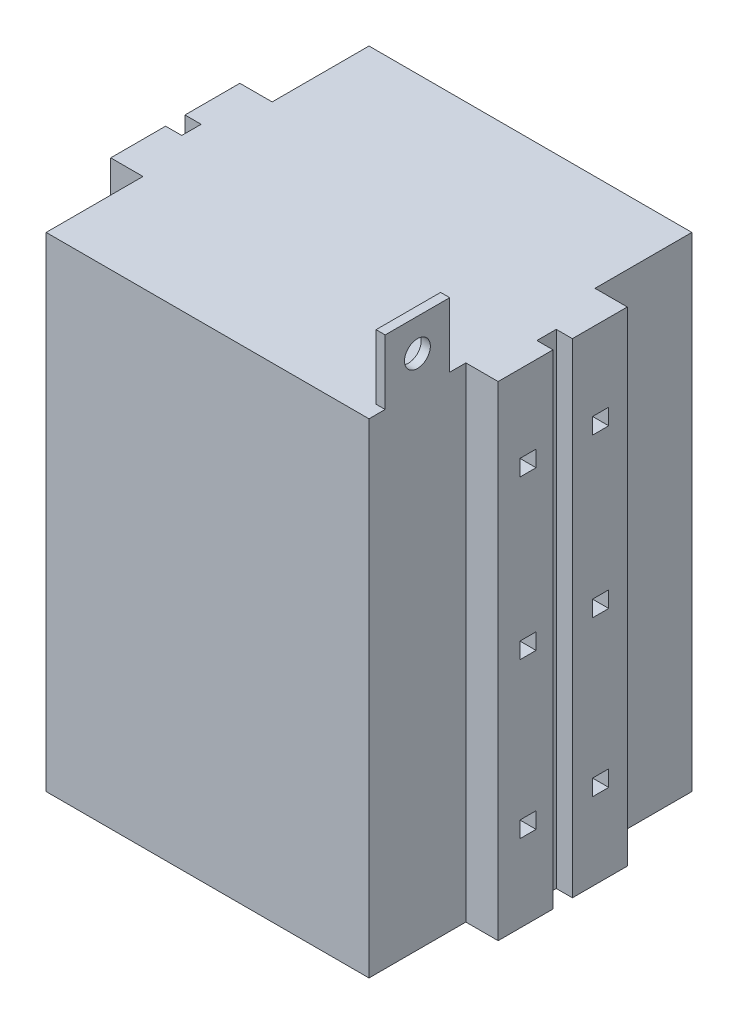
SolidWorks part; units mm, degrees
ref_plane "Plan de face" through (0, 0, 0) normal (0, 0, 1) x (1, 0, 0)
ref_plane "Plan de dessus" through (0, 0, 0) normal (0, 1, 0) x (1, 0, 0)
ref_plane "Plan de droite" through (0, 0, 0) normal (1, 0, 0) x (0, 0, -1)
sketch "Esquisse1" plane through (0, 0, 0) normal (0, 0, 1) x (1, 0, 0)
  line L1 (0, 0) -> (100, 0)
  line L2 (0, 0) -> (0, 150)
  line L3 (0, 150) -> (100, 150)
  line L4 (100, 0) -> (100, 150)
  dimension "D1" = 150
  dimension "D2" = 100
extrude "Boss.-Extru.1" add sketch "Esquisse1" along normal blind 100
sketch "Esquisse2" plane through (0, 0, 0) normal (0, 0, -1) x (-1, 0, 0)
  line L0 (0, 0) -> (-100, 0) construction
  line L1 (-5, 5) -> (-95, 5)
  line L2 (-5, 5) -> (-5, 145)
  line L3 (-5, 145) -> (-95, 145)
  line L4 (-95, 5) -> (-95, 145)
  line L5 (-100, 0) -> (-100, 150) construction
  dimension "D1" = 90
  dimension "D2" = 140
  dimension "D3" = 5
  dimension "D4" = 5
extrude "Enlèv. mat.-Extru.1" cut sketch "Esquisse2" against normal blind 95
sketch "Esquisse4" plane through (0, 0, 0) normal (-1, 0, 0) x (0, 0, 1)
  line L0 (100, 0) -> (0, 0) construction
  line L1 (30, 0) -> (70, 0)
  line L2 (30, 0) -> (30, 150)
  line L3 (30, 150) -> (70, 150)
  line L4 (70, 0) -> (70, 150)
  line L5 (100, 150) -> (0, 150) construction
  line L6 (0, 150) -> (0, 0) construction
  dimension "D1" = 40
  dimension "D2" = 30
extrude "Boss.-Extru.2" add sketch "Esquisse4" along normal blind 10
sketch "Esquisse5" plane through (-10, 0, 0) normal (-1, 0, 0) x (0, 0, 1)
  line L0 (30, 0) -> (70, 0) construction
  line L1 (47, 0) -> (53, 0)
  line L2 (47, 0) -> (47, 150)
  line L3 (47, 150) -> (53, 150)
  line L4 (53, 0) -> (53, 150)
  line L5 (70, 150) -> (30, 150) construction
  line L6 (30, 150) -> (30, 0) construction
  dimension "D1" = 6
  dimension "D2" = 17
extrude "Enlèv. mat.-Extru.2" cut sketch "Esquisse5" against normal blind 5
sketch "Esquisse7" plane through (100, 0, 0) normal (1, 0, 0) x (0, 0, -1)
  line L1 (-70, 0) -> (-30, 0)
  line L2 (-70, 0) -> (-70, 150)
  line L3 (-70, 150) -> (-30, 150)
  line L4 (-30, 0) -> (-30, 150)
extrude "Boss.-Extru.3" add sketch "Esquisse7" along normal blind 10
sketch "Esquisse8" plane through (110, 0, 0) normal (1, 0, 0) x (0, 0, -1)
  line L1 (-53, 0) -> (-47, 0)
  line L2 (-53, 0) -> (-53, 150)
  line L3 (-53, 150) -> (-47, 150)
  line L4 (-47, 0) -> (-47, 150)
extrude "Enlèv. mat.-Extru.3" cut sketch "Esquisse8" against normal blind 5
sketch "Esquisse9" plane through (110, 0, 0) normal (1, 0, 0) x (0, 0, -1)
  line L0 (-30, 150) -> (-47, 150) construction
  line L1 (-40.75, 126) -> (-35.75, 126)
  line L2 (-40.75, 126) -> (-40.75, 121)
  line L3 (-40.75, 121) -> (-35.75, 121)
  line L4 (-35.75, 126) -> (-35.75, 121)
  line L5 (-40.75, 77) -> (-35.75, 77)
  line L6 (-40.75, 77) -> (-40.75, 72)
  line L7 (-40.75, 72) -> (-35.75, 72)
  line L8 (-35.75, 77) -> (-35.75, 72)
  line L9 (-40.75, 29) -> (-35.75, 29)
  line L10 (-40.75, 29) -> (-40.75, 24)
  line L11 (-40.75, 24) -> (-35.75, 24)
  line L12 (-35.75, 29) -> (-35.75, 24)
  line L13 (-47, 0) -> (-30, 0) construction
  line L14 (-47, 0) -> (-47, 150) construction
  line L17 (-49.5, 0) -> (-49.5, 150)
  line L18 (-47, 0) -> (-47, 150) construction
  line L20 (-58.25, 29) -> (-63.25, 29)
  line L21 (-63.25, 29) -> (-63.25, 24)
  line L22 (-58.25, 29) -> (-58.25, 24)
  line L23 (-58.25, 24) -> (-63.25, 24)
  line L24 (-63.25, 77) -> (-63.25, 72)
  line L25 (-58.25, 77) -> (-63.25, 77)
  line L26 (-58.25, 77) -> (-58.25, 72)
  line L27 (-58.25, 72) -> (-63.25, 72)
  line L28 (-58.25, 126) -> (-63.25, 126)
  line L29 (-63.25, 126) -> (-63.25, 121)
  line L30 (-58.25, 121) -> (-63.25, 121)
  line L31 (-58.25, 126) -> (-58.25, 121)
  dimension "D1" = 5
  dimension "D2" = 5
  dimension "D3" = 24
  dimension "D4" = 5
  dimension "D5" = 5
  dimension "D6" = 24
  dimension "D7" = 5
  dimension "D8" = 5
  dimension "D9" = 73
  dimension "D10" = 6.25
  dimension "D11" = 6.25
  dimension "D12" = 6.25
  dimension "D13" = 2.5
  dimension "D14" = 150
extrude "Enlèv. mat.-Extru.4" cut sketch "Esquisse9" against normal through all contours L4 L1 L2 L3 | L27 L26 L25 L24 | L8 L5 L6 L7 | L23 L22 L20 L21 | L28 L29 L30 L31 | L10 L11 L12 L9
sketch "Esquisse10" plane through (0, 150, 0) normal (0, 1, 0) x (1, 0, 0)
  line L0 (100, -100) -> (100, -70) construction
  line L1 (100, -75) -> (97.1831, -75)
  line L2 (100, -75) -> (100, -95)
  line L3 (100, -95) -> (97.1831, -95)
  line L4 (97.1831, -75) -> (97.1831, -95)
  line L5 (110, -70) -> (100, -70) construction
  point P6 (98.5916, -75)
  dimension "D1" = 20
  dimension "D2" = 5
extrude "Boss.-Extru.4" add sketch "Esquisse10" along normal blind 20
sketch "Esquisse11" plane through (100, 0, 0) normal (1, 0, 0) x (0, 0, -1)
  line L0 (-95, 170) -> (-75, 170) construction
  line L1 (-95, 170) -> (-95, 150) construction
  circle A0 centre (-85, 160) radius 4
  dimension "D1" = 8
  dimension "D2" = 10
  dimension "D3" = 10
extrude "Enlèv. mat.-Extru.5" cut sketch "Esquisse11" against normal through all
